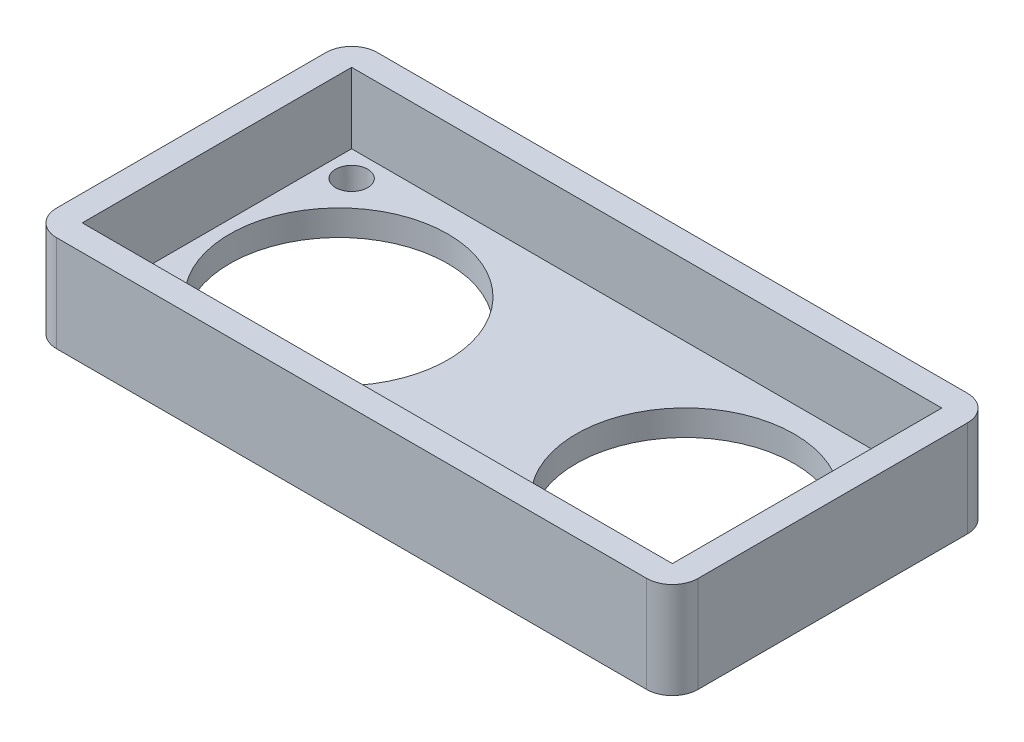
SolidWorks part; units mm, degrees
ref_plane "前视基准面" through (0, 0, 0) normal (0, 0, 1) x (1, 0, 0)
ref_plane "上视基准面" through (0, 0, 0) normal (0, 1, 0) x (1, 0, 0)
ref_plane "右视基准面" through (0, 0, 0) normal (1, 0, 0) x (0, 0, -1)
other "Configuration Table"
sketch "草图1" plane through (0, 0, 0) normal (0, 1, 0) x (1, 0, 0)
  line L1 (-23, 12.5) -> (23, 12.5)
  line L2 (-25, 10.5) -> (-25, -10.5)
  line L3 (-23, -12.5) -> (23, -12.5)
  line L4 (25, 10.5) -> (25, -10.5)
  line L5 (-25, 12.5) -> (25, -12.5) construction
  line L6 (-25, -12.5) -> (25, 12.5) construction
  arc A0 (-23, 12.5) -> (-25, 10.5) centre (-23, 10.5) ccw
  arc A1 (-25, -10.5) -> (-23, -12.5) centre (-23, -10.5) ccw
  arc A2 (25, 10.5) -> (23, 12.5) centre (23, 10.5) ccw
  arc A3 (23, -12.5) -> (25, -10.5) centre (23, -10.5) ccw
  point P0 (0, 0)
  dimension "D3" = 4
  dimension "D4" = 4
  dimension "D5" = 4
  dimension "D6" = 4
  dimension "D1" = 50
  dimension "D2" = 25
extrude "凸台-拉伸1" add sketch "草图1" along normal blind 2
sketch "草图2" plane through (0, 2, 0) normal (0, 1, 0) x (1, 0, 0)
  line L0 (23, 12.5) -> (-23, 12.5) construction
  line L1 (-23, 10.5) -> (23, 10.5)
  line L2 (-23, 10.5) -> (-23, -10.5)
  line L3 (-23, -10.5) -> (23, -10.5)
  line L4 (23, 10.5) -> (23, -10.5)
  line L5 (-23, 10.5) -> (23, -10.5) construction
  line L6 (-23, -10.5) -> (23, 10.5) construction
  line L7 (-25, 10.5) -> (-25, -10.5) construction
  line L12 (23, 12.5) -> (-23, 12.5)
  line L13 (-25, 10.5) -> (-25, -10.5)
  line L14 (-23, -12.5) -> (23, -12.5)
  line L15 (25, -10.5) -> (25, 10.5)
  line L16 (23, 12.5) -> (-23, 12.5)
  line L17 (-25, 10.5) -> (-25, -10.5)
  line L18 (-23, -12.5) -> (23, -12.5)
  line L19 (25, -10.5) -> (25, 10.5)
  arc A4 (25, 10.5) -> (23, 12.5) centre (23, 10.5) ccw
  arc A5 (-23, 12.5) -> (-25, 10.5) centre (-23, 10.5) ccw
  arc A6 (-25, -10.5) -> (-23, -12.5) centre (-23, -10.5) ccw
  arc A7 (23, -12.5) -> (25, -10.5) centre (23, -10.5) ccw
  arc A8 (25, 10.5) -> (23, 12.5) centre (23, 10.5) ccw
  arc A9 (-23, 12.5) -> (-25, 10.5) centre (-23, 10.5) ccw
  arc A10 (-25, -10.5) -> (-23, -12.5) centre (-23, -10.5) ccw
  arc A11 (23, -12.5) -> (25, -10.5) centre (23, -10.5) ccw
  point P0 (0, 0)
  dimension "D1" = 2
  dimension "D2" = 2
  dimension "D3" = 0
extrude "凸台-拉伸2" add sketch "草图2" along normal blind 5.5
sketch "草图3" plane through (0, 0, 0) normal (0, -1, 0) x (1, 0, 0)
  line L0 (-23, 12.5) -> (23, 12.5) construction
  line L1 (-25, -10.5) -> (-25, 10.5) construction
  line L2 (23, -12.5) -> (-23, -12.5) construction
  line L3 (25, 10.5) -> (25, -10.5) construction
  circle A0 centre (-21, 8.5) radius 1.25
  circle A1 centre (-21, -8.5) radius 1.25
  circle A2 centre (21, 8.5) radius 1.25
  circle A3 centre (21, -8.5) radius 1.25
  dimension "D3" = 4
  dimension "D4" = 4
  dimension "D5" = 4
  dimension "D6" = 4
  dimension "2.5" = 2.5
  dimension "D9" = 4
  dimension "D10" = 2.5
  dimension "D11" = 2.5
  dimension "D12" = 2.5
  dimension "D1" = 4
  dimension "D2" = 4
  dimension "D8" = 4
extrude "切除-拉伸1" cut sketch "草图3" against normal through all
sketch "草图4" plane through (0, 0, 0) normal (0, -1, 0) x (1, 0, 0)
  circle A0 centre (-13.5, 0) radius 8.5
  circle A1 centre (13.5, 0) radius 8.5
  dimension "D1" = 17
  dimension "D2" = 17
  dimension "D3" = 27
  dimension "D4" = 13.5
extrude "切除-拉伸2" cut sketch "草图4" against normal through all
